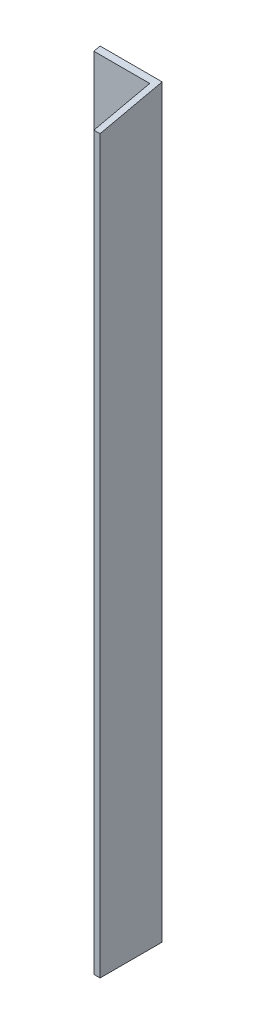
SolidWorks part; units mm, degrees
material "AISI 1020"
ref_plane "Front Plane" through (0, 0, 0) normal (0, 0, 1) x (1, 0, 0)
ref_plane "Top Plane" through (0, 0, 0) normal (0, 1, 0) x (1, 0, 0)
ref_plane "Right Plane" through (0, 0, 0) normal (1, 0, 0) x (0, 0, -1)
sketch "Sketch1" plane through (0, 0, 0) normal (0, 0, 1) x (1, 0, 0)
  line L1 (-61.4627, 118.1642) -> (-41.4627, 118.1642)
  line L2 (-61.4627, 118.1642) -> (-61.4627, -121.8358)
  line L3 (-61.4627, -121.8358) -> (-41.4627, -121.8358)
  line L4 (-41.4627, 118.1642) -> (-41.4627, -121.8358)
  dimension "D1" = 240
  dimension "D2" = 20
extrude "Boss-Extrude1" add sketch "Sketch1" against normal blind 20
sketch "Sketch2" plane through (-61.4627, 0, 0) normal (-1, 0, 0) x (0, 0, 1)
  line L0 (-20, 118.1642) -> (0, 113.6936)
  line L1 (0, 118.1642) -> (0, -121.8358) construction
  line L2 (0, 113.6936) -> (0, 118.1642)
  line L3 (0, 118.1642) -> (-20, 118.1642)
extrude "Cut-Extrude1" cut sketch "Sketch2" against normal blind 20
sketch "Sketch3" plane through (0, -121.8358, 0) normal (0, -1, 0) x (1, 0, 0)
  line L1 (-61.4627, 0) -> (-43.4627, 0)
  line L2 (-61.4627, 0) -> (-61.4627, -18)
  line L3 (-61.4627, -18) -> (-43.4627, -18)
  line L4 (-43.4627, 0) -> (-43.4627, -18)
  dimension "D1" = 18
  dimension "D2" = 18
extrude "Cut-Extrude2" cut sketch "Sketch3" against normal blind 290
